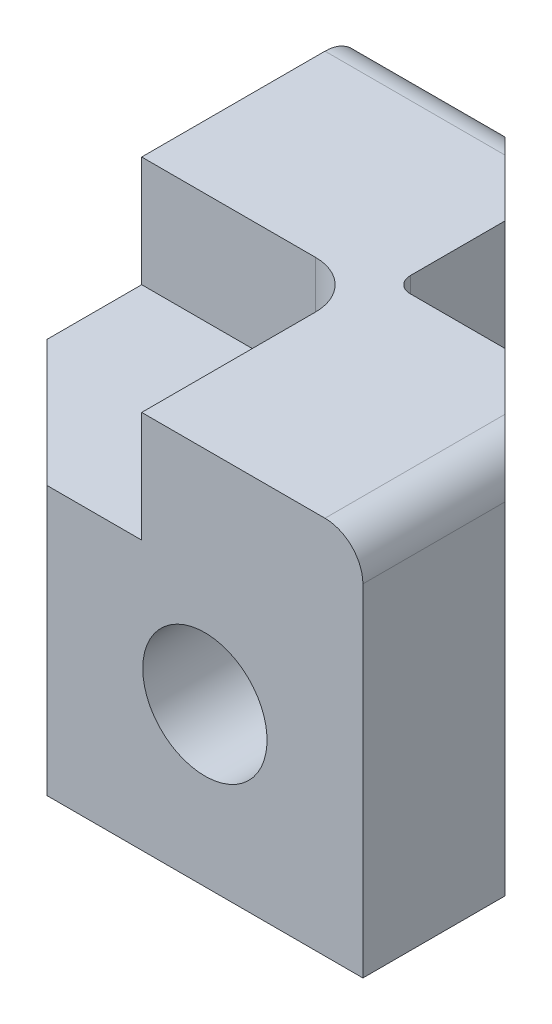
SolidWorks part; units mm, degrees
other "Markup1"
sketch "Sketch99" plane through (-25.4, 44.45, 25.4) normal (-0.9303, 0.3601, 0.0694) x (0.0764, 0.0053, 0.9971)
material "6061-T6 (SS)"
ref_plane "Front Plane" through (0, 0, 0) normal (0, 0, 1) x (1, 0, 0)
ref_plane "Top Plane" through (0, 0, 0) normal (0, 1, 0) x (1, 0, 0)
ref_plane "Right Plane" through (0, 0, 0) normal (1, 0, 0) x (0, 0, -1)
sketch "Sketch7" plane through (0, 0, 0) normal (0, 1, 0) x (1, 0, 0)
  line L0 (0, 0) -> (11.1125, 0)
  line L1 (20.6375, -9.525) -> (20.6375, -23.8125)
  line L2 (20.6375, -23.8125) -> (-23.8125, -23.8125)
  line L3 (-23.8125, -23.8125) -> (0, 0)
  line L4 (11.1125, 0) -> (20.6375, -9.525)
  dimension "D1" = 45
  dimension "D2" = 44.45
  dimension "D3" = 23.8125
  dimension "D4" = 14.2875
  dimension "D5" = 45
extrude "Boss-Extrude2" add sketch "Sketch7" along normal blind 38.1
sketch "Sketch22" plane through (0, 0, 23.8125) normal (0, 0, 1) x (1, 0, 0)
  line L1 (20.6375, 38.1) -> (20.6375, 0) construction
  line L2 (-23.8125, 0) -> (20.6375, 0) construction
  point P0 (4.7625, 15.875)
  dimension "D1" = 15.875
  dimension "D2" = 15.875
sketch "Sketch23" plane through (0, 0, 0) normal (0, 0, -1) x (-1, 0, 0)
  point P0 (-4.7625, 15.875)
curve "Curve3"
sketch3d "3DSketch6"
  line L0 (4.7625, 15.875, 23.8125) -> (4.7625, 15.875, 0) construction
sketch "Sketch24" plane through (4.7625, 0, 0) normal (-1, 0, 0) x (0, 0, 1)
  line L10 (10.3505, 15.875) -> (23.8125, 15.875)
  line L12 (10.3505, 15.875) -> (10.3505, 22.1178)
  line L13 (10.3505, 22.1178) -> (23.8125, 22.1178)
  line L14 (23.8125, 15.875) -> (23.8125, 22.1178)
  dimension "D2" = 6.2428
  dimension "D10" = 13.462
revolve "Port Manifold" cut sketch "Sketch24" angle 360 about L10
mirror "Mirror6" of "Port Manifold", "Boss-Extrude2"
fillet "Fillet16" radius 3.81 2 edges at (-16.6687, 38.1, -20.6375) (20.6375, 38.1, 16.6687)
sketch "Sketch93" plane through (0, 38.1, 0) normal (0, 1, 0) x (1, 0, 0)
  line L1 (-23.8125, -23.8125) -> (-1.5875, -23.8125)
  line L2 (-23.8125, -23.8125) -> (-23.8125, -1.5875)
  line L3 (-23.8125, -1.5875) -> (-6.35, -1.5875)
  line L4 (-1.5875, -23.8125) -> (-1.5875, -6.35)
  line L5 (-23.8125, -23.8125) -> (-23.8125, 16.8275) construction
  line L7 (-23.8125, -23.8125) -> (16.8275, -23.8125) construction
  arc A0 (-6.35, -1.5875) -> (-1.5875, -6.35) centre (-6.35, -6.35) cw
  dimension "D2" = 4.7625
  dimension "D3" = 22.225
extrude "Cut-Extrude3" cut sketch "Sketch93" against normal blind 11.1125
ref_plane "Plane1" through (0, 0, 0) normal (0.7071, 0, 0.7071) x (0.7071, 0, -0.7071)
ref_plane "Plane2" through (0, 15.875, 0) normal (0, 1, 0) x (1, 0, 0)
sketch "Sketch101" plane through (0, 0, 0) normal (0, -1, 0) x (1, 0, 0)
  line L0 (0, 0) -> (-23.8125, 23.8125) construction
  line L1 (-23.8125, 23.8125) -> (20.6375, 23.8125) construction
  circle A0 centre (-9.8425, 9.8425) radius 2.54
  dimension "D1" = 5.08
  dimension "D2" = 13.97
extrude "Cut-Extrude4" cut sketch "Sketch101" against normal blind 17.78
sketch "Sketch102" plane through (0, 15.875, 0) normal (0, 1, 0) x (1, 0, 0)
  line L0 (-0.4445, -9.3345) -> (-9.176, -9.3345) construction
  line L5 (-0.4445, -9.3345) -> (-10.6045, -9.3345)
  line L6 (-0.4445, -9.3345) -> (-0.4445, -10.6045)
  line L7 (-0.4445, -10.6045) -> (-10.6045, -10.6045)
  line L8 (-10.6045, -9.3345) -> (-10.6045, -10.6045)
  dimension "D1" = 5.207
  dimension "D2" = 14.478
  dimension "D3" = 13.208
  dimension "D4" = 10.16
revolve "Cut-Revolve1" cut sketch "Sketch102" angle 360 about L0
mirror "Mirror10" about plane through (0, 0, 0) normal (0.7071, 0, 0.7071) of "Cut-Revolve1"
chamfer "Chamfer1" distance 12.7 1 edges at (-23.8125, 13.4938, 23.8125)
fillet "Fillet17" radius 1.5875 1 edges at (0, 19.05, 0)
